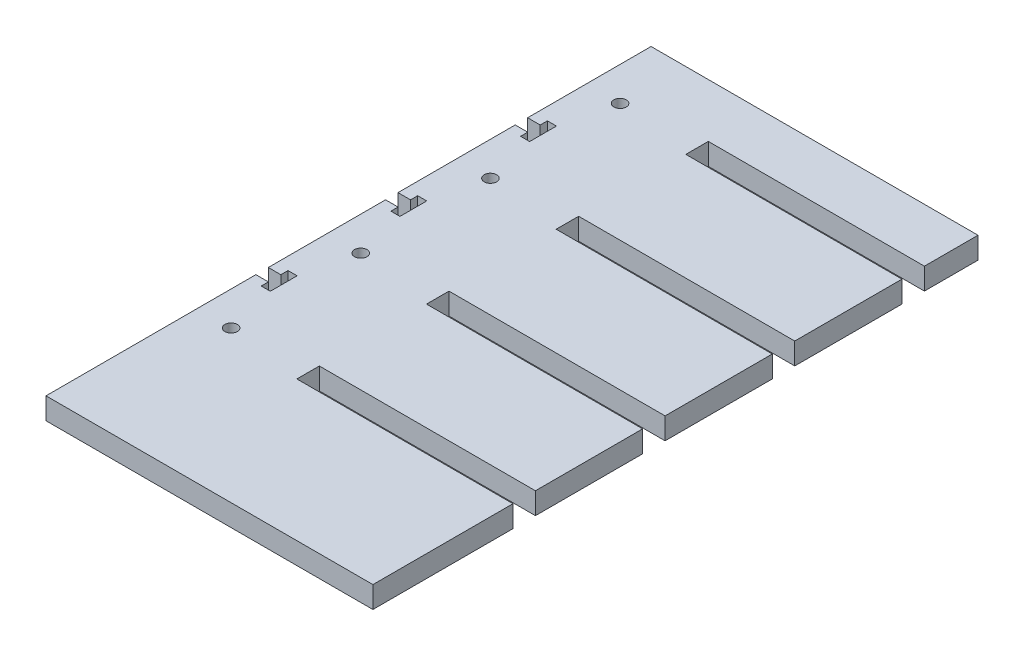
SolidWorks part; units mm, degrees
ref_plane "Front Plane" through (0, 0, 0) normal (0, 0, 1) x (1, 0, 0)
ref_plane "Top Plane" through (0, 0, 0) normal (0, 1, 0) x (1, 0, 0)
ref_plane "Right Plane" through (0, 0, 0) normal (1, 0, 0) x (0, 0, -1)
sketch "Sketch1" plane through (0, 0, 0) normal (0, 1, 0) x (1, 0, 0)
  line L0 (-38.1, 69.85) -> (-38.1, -88.9) construction
  line L1 (-48.0314, 88.9) -> (48.0314, 88.9)
  line L2 (-48.0314, 88.9) -> (-48.0314, 52.6288)
  line L3 (-48.0314, -88.9) -> (48.0314, -88.9)
  line L4 (48.0314, 88.9) -> (48.0314, 73.152)
  line L5 (-48.0314, 88.9) -> (48.0314, -88.9) construction
  line L6 (-48.0314, -88.9) -> (48.0314, 88.9) construction
  line L7 (-38.1, 69.85) -> (48.0314, 69.85) construction
  line L8 (48.0314, 73.152) -> (-15.4686, 73.152)
  line L9 (48.0314, 66.548) -> (-15.4686, 66.548)
  line L10 (-15.4686, 73.152) -> (-15.4686, 66.548)
  line L11 (48.0314, 66.548) -> (48.0314, 35.052)
  line L12 (48.0314, 28.448) -> (-15.4686, 28.448)
  line L13 (-15.4686, 35.052) -> (-15.4686, 28.448)
  line L14 (48.0314, 35.052) -> (-15.4686, 35.052)
  line L15 (48.0314, -9.652) -> (-15.4686, -9.652)
  line L16 (-15.4686, -3.048) -> (-15.4686, -9.652)
  line L17 (48.0314, -3.048) -> (-15.4686, -3.048)
  line L18 (48.0314, -47.752) -> (-15.4686, -47.752)
  line L19 (-15.4686, -41.148) -> (-15.4686, -47.752)
  line L20 (48.0314, -41.148) -> (-15.4686, -41.148)
  line L21 (48.0314, 28.448) -> (48.0314, -3.048)
  line L22 (48.0314, -9.652) -> (48.0314, -41.148)
  line L23 (48.0314, -47.752) -> (48.0314, -88.9)
  line L24 (-38.1, 69.85) -> (-38.1, 31.75) construction
  line L25 (-38.1, 50.8) -> (-48.0314, 50.8) construction
  line L26 (-48.0314, 52.6288) -> (-44.3484, 52.6288)
  line L27 (-44.3484, 52.6288) -> (-44.3484, 54.737)
  line L28 (-44.3484, 54.737) -> (-41.6814, 54.737)
  line L29 (-41.6814, 54.737) -> (-41.6814, 46.863)
  line L30 (-44.3484, 46.863) -> (-41.6814, 46.863)
  line L31 (-44.3484, 48.9712) -> (-44.3484, 46.863)
  line L32 (-48.0314, 48.9712) -> (-44.3484, 48.9712)
  line L33 (-48.0314, 14.5288) -> (-44.3484, 14.5288)
  line L34 (-48.0314, 10.8712) -> (-44.3484, 10.8712)
  line L35 (-44.3484, 10.8712) -> (-44.3484, 8.763)
  line L36 (-44.3484, 8.763) -> (-41.6814, 8.763)
  line L37 (-41.6814, 16.637) -> (-41.6814, 8.763)
  line L38 (-44.3484, 16.637) -> (-41.6814, 16.637)
  line L39 (-44.3484, 14.5288) -> (-44.3484, 16.637)
  line L40 (-48.0314, -23.5712) -> (-44.3484, -23.5712)
  line L41 (-48.0314, -27.2288) -> (-44.3484, -27.2288)
  line L42 (-44.3484, -27.2288) -> (-44.3484, -29.337)
  line L43 (-44.3484, -29.337) -> (-41.6814, -29.337)
  line L44 (-41.6814, -21.463) -> (-41.6814, -29.337)
  line L45 (-44.3484, -21.463) -> (-41.6814, -21.463)
  line L46 (-44.3484, -23.5712) -> (-44.3484, -21.463)
  line L47 (-48.0314, 48.9712) -> (-48.0314, 14.5288)
  line L48 (-48.0314, 10.8712) -> (-48.0314, -23.5712)
  line L49 (-48.0314, -27.2288) -> (-48.0314, -88.9)
  circle A0 centre (-38.1, 69.85) radius 1.8288
  circle A1 centre (-38.1, 31.75) radius 1.8288
  circle A2 centre (-38.1, -6.35) radius 1.8288
  circle A3 centre (-38.1, -44.45) radius 1.8288
  point P0 (0, 0)
  point P40 (-41.6814, 50.8)
  dimension "D9" = 3.6576
  dimension "D1" = 177.8
  dimension "D2" = 96.0628
  dimension "D3" = 9.9314
  dimension "D4" = 19.05
  dimension "D6" = 3.302
  dimension "D7" = 63.5
  dimension "D10" = 3.6576
  dimension "D11" = 6.35
  dimension "D12" = 2.667
  dimension "D13" = 7.874
  dimension "D14" = 19.05
  dimension "D5" = 4
  dimension "D8" = 4
  dimension "D15" = 3
extrude "Boss-Extrude1" add sketch "Sketch1" against normal blind 6.35
